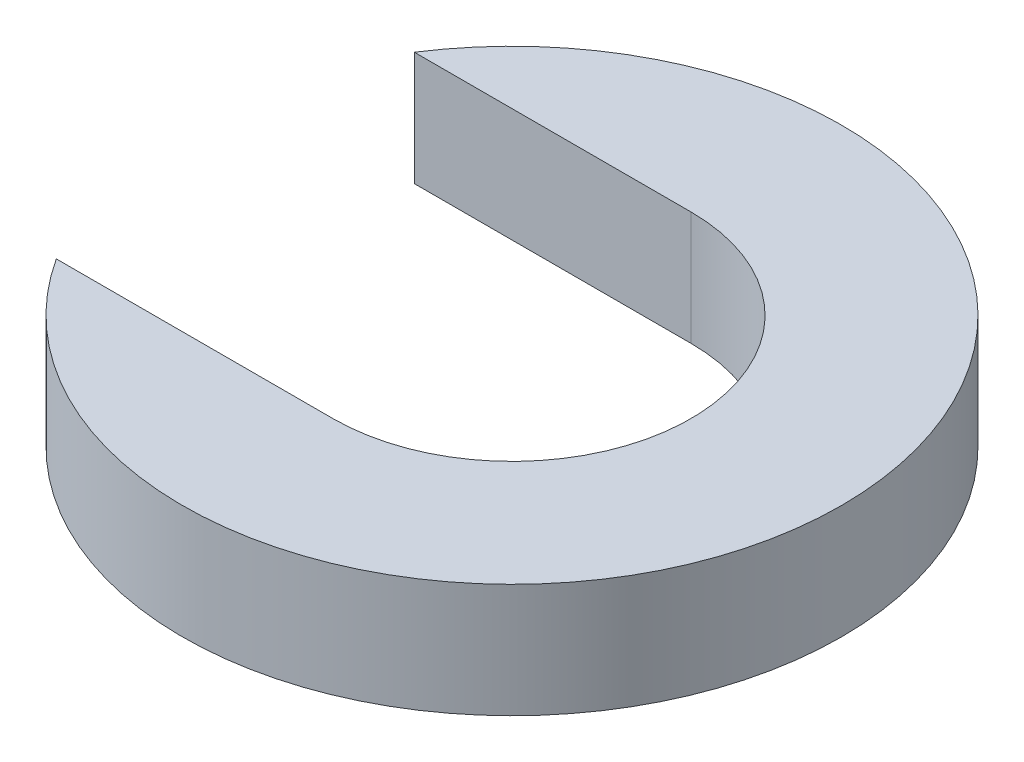
SolidWorks part; units mm, degrees
ref_plane "Front Plane" through (0, 0, 0) normal (0, 0, 1) x (1, 0, 0)
ref_plane "Top Plane" through (0, 0, 0) normal (0, 1, 0) x (1, 0, 0)
ref_plane "Right Plane" through (0, 0, 0) normal (1, 0, 0) x (0, 0, -1)
sketch "Sketch2" plane through (0, 0, 0) normal (0, 1, 0) x (1, 0, 0)
  line L1 (0, 4.953) -> (-7.6562, 4.953)
  line L3 (-7.6562, -4.953) -> (0, -4.953)
  arc A0 (0, -4.953) -> (0, 4.953) centre (0, 0) ccw
  arc A1 (-7.6562, -4.953) -> (-7.6562, 4.953) centre (0, 0) ccw
  dimension "D1" = 9.906
  dimension "D2" = 18.2372
extrude "Boss-Extrude1" add sketch "Sketch2" along normal blind 3.1496
